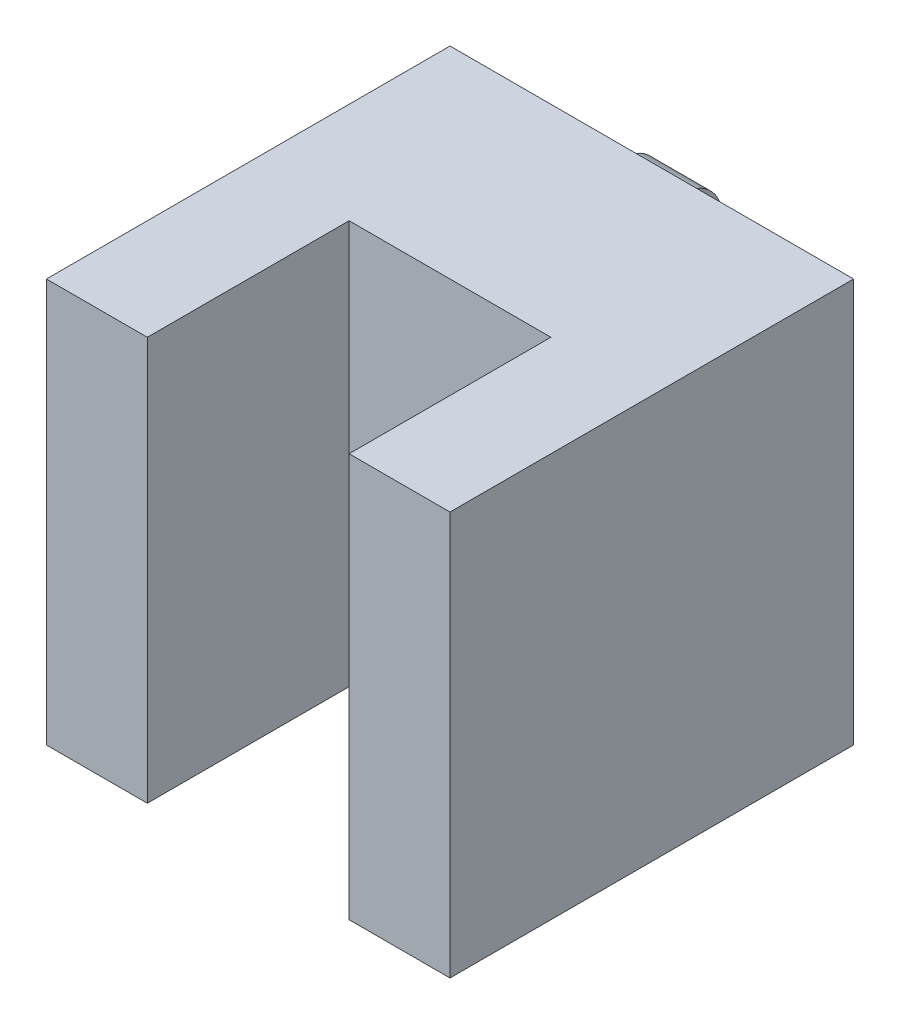
SolidWorks part; units mm, degrees
ref_plane "Front Plane" through (0, 0, 0) normal (0, 0, 1) x (1, 0, 0)
ref_plane "Top Plane" through (0, 0, 0) normal (0, 1, 0) x (1, 0, 0)
ref_plane "Right Plane" through (0, 0, 0) normal (1, 0, 0) x (0, 0, -1)
sketch "Sketch1" plane through (0, 0, 0) normal (0, 1, 0) x (1, 0, 0)
  line L0 (0, 0) -> (0, 10)
  line L1 (0, 0) -> (-5, 0)
  line L2 (-5, 0) -> (-5, 20)
  line L3 (0, 10) -> (10, 10)
  line L4 (10, 10) -> (10, 0)
  line L5 (10, 0) -> (15, 0)
  line L6 (15, 0) -> (15, 20)
  line L7 (-5, 20) -> (15, 20)
  dimension "D1" = 10
  dimension "D2" = 5
  dimension "D3" = 20
  dimension "D4" = 10
  dimension "D5" = 5
  dimension "D6" = 20
extrude "Boss-Extrude1" add sketch "Sketch1" along normal blind 20
ref_plane "Plane1" through (5, 0, 0) normal (1, 0, 0) x (0, 0, -1)
sketch "Sketch3" plane through (5, 0, 0) normal (1, 0, 0) x (0, 0, -1)
  line L0 (20, 20) -> (20, 0) construction
  line L1 (20, 18.9127) -> (20, 19.4127)
  line L2 (20, 15.9127) -> (20, 15.4127)
  arc A0 (20, 15.4127) -> (20, 19.4127) centre (20, 17.4127) ccw
  arc A1 (20, 15.9127) -> (20, 18.9127) centre (20, 17.4127) ccw
  dimension "D1" = 3
extrude "Boss-Extrude2" add sketch "Sketch3" along normal blind 1.5 and the other way blind 1.5
